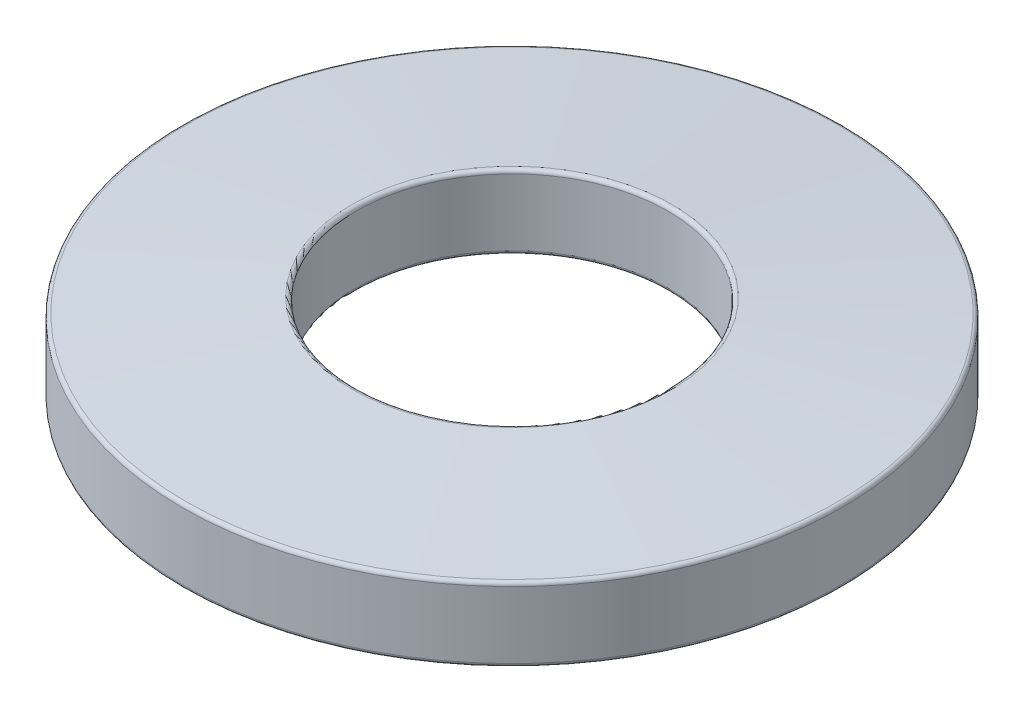
SolidWorks part; units mm, degrees
ref_plane "Front Plane" through (0, 0, 0) normal (0, 0, 1) x (1, 0, 0)
ref_plane "Top Plane" through (0, 0, 0) normal (0, 1, 0) x (1, 0, 0)
ref_plane "Right Plane" through (0, 0, 0) normal (1, 0, 0) x (0, 0, -1)
sketch "Sketch2" plane through (0, 0, 0) normal (1, 0, 0) x (0, 0, -1)
  line L0 (-10.5791, 0) -> (10.5791, 0) construction
  line L1 (10.5791, 6.0325) -> (10.5791, 1.0033)
  line L2 (10.5791, 0) -> (22.352, 0) construction
  line L3 (10.5791, 0) -> (10.5791, 6.0325) construction
  line L4 (10.5791, 6.0325) -> (22.352, 6.0325) construction
  line L5 (22.352, 0) -> (22.352, 6.0325) construction
  line L6 (22.352, 0) -> (22.352, 5.0292)
  line L7 (10.5791, 6.0325) -> (22.352, 5.0292)
  line L8 (22.352, 0) -> (10.5791, 1.0033)
  line L9 (0, 0) -> (0, 11.9435) construction
  point P4 (0, 0)
  dimension "D1" = 21.1582
  dimension "D2" = 22.352
  dimension "D3" = 6.0325
  dimension "D4" = 5.0292
  dimension "D5" = 5.0292
revolve "Revolve1" add sketch "Sketch2" angle 360 about L9
fillet "Fillet1" radius 0.254 4 edges at (0, 0, -22.352) (0, 5.0292, -22.352) (0, 1.0033, -10.5791) (0, 6.0325, -10.5791)
